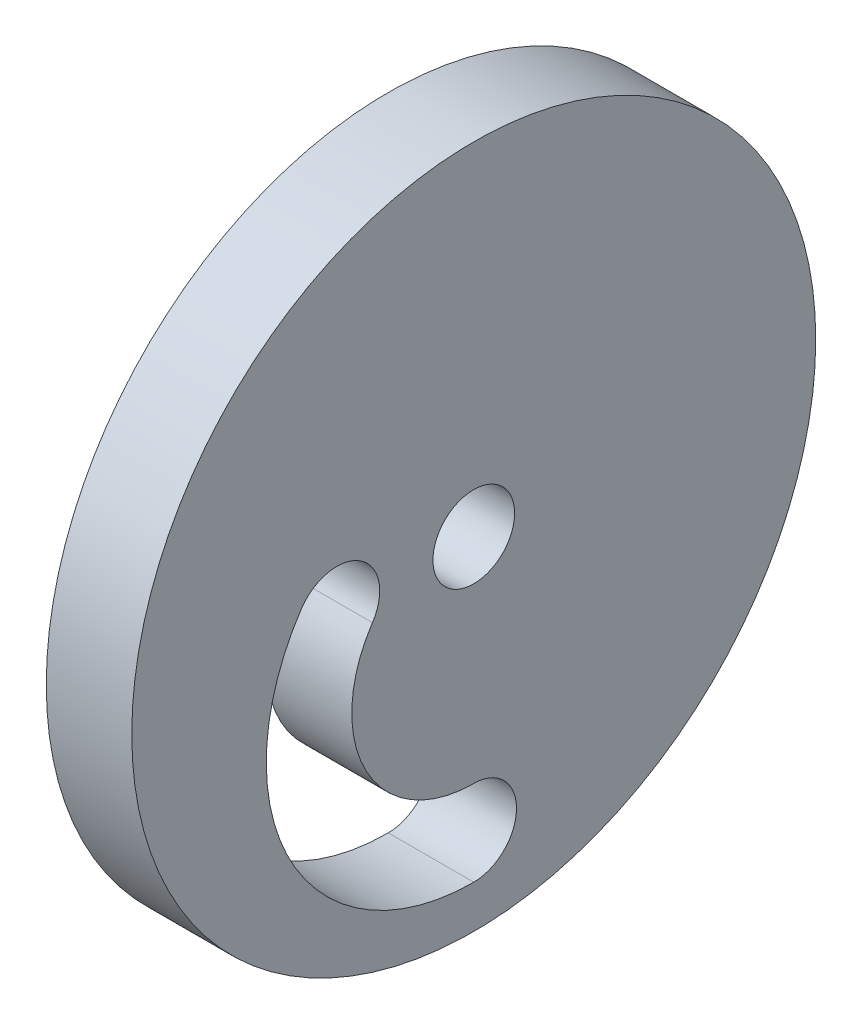
SolidWorks part; units mm, degrees
ref_plane "Front Plane" through (0, 0, 0) normal (0, 0, 1) x (1, 0, 0)
ref_plane "Top Plane" through (0, 0, 0) normal (0, 1, 0) x (1, 0, 0)
ref_plane "Right Plane" through (0, 0, 0) normal (1, 0, 0) x (0, 0, -1)
sketch "Sketch1" plane through (0, 0, 0) normal (1, 0, 0) x (0, 0, -1)
  line L0 (0, 25.4) -> (0, -25.4) construction
  line L1 (-25.4, 0) -> (25.4, 0) construction
  line L2 (-18.2261, -22.225) -> (18.2261, -22.225) construction
  circle A0 centre (0, 0) radius 3.0314
  circle A1 centre (0, 0) radius 25.4
  arc A4 (0, -19.05) -> (-10.16, 0) centre (0, -6.8157) cw construction
  arc A5 (-12.7967, 1.7688) -> (0, -22.225) centre (0, -6.8157) ccw
  arc A6 (-7.5233, -1.7688) -> (0, -15.875) centre (0, -6.8157) ccw
  arc A7 (-7.5233, -1.7688) -> (-12.7967, 1.7688) centre (-10.16, 0) ccw
  arc A8 (0, -22.225) -> (0, -15.875) centre (0, -19.05) ccw
  point P10 (0, 0)
  point P11 (0, 0)
  point P13 (-10.795, -12.573)
  point P18 (-10.16, 0)
  point P24 (0, -22.225)
  dimension "D1" = 50.8
  dimension "D6" = 3.175
  dimension "D2" = 19.05
  dimension "D3" = 10.16
extrude "Boss-Extrude1" add sketch "Sketch1" along normal blind 6.35
